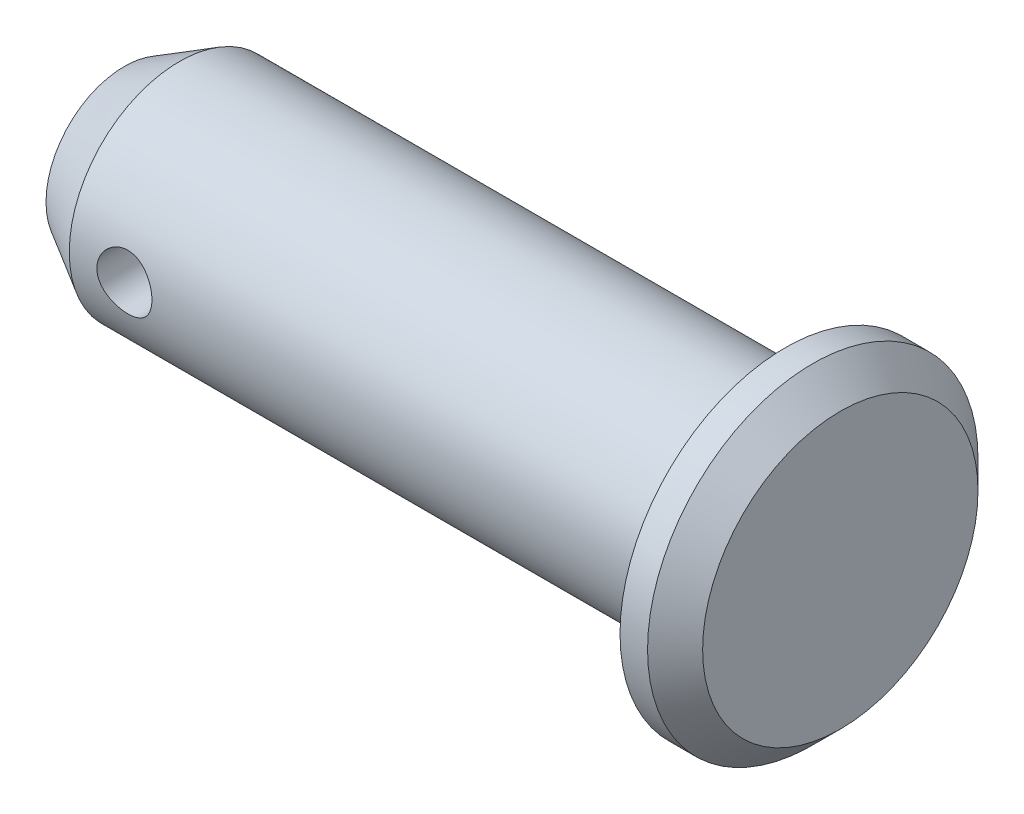
SolidWorks part; units mm, degrees
material "Plain Carbon Steel"
ref_plane "Front" through (0, 0, 0) normal (0, 0, 1) x (1, 0, 0)
ref_plane "Top" through (0, 0, 0) normal (0, 1, 0) x (1, 0, 0)
ref_plane "Right" through (0, 0, 0) normal (1, 0, 0) x (0, 0, -1)
sketch "Sketch1" plane through (0, 0, 0) normal (0, 0, 1) x (1, 0, 0)
  line L0 (0, 0) -> (-74.8754, 0) construction
  line L1 (0, 0) -> (-12, 0)
  line L2 (0, 0) -> (0, 2)
  line L3 (0, 2) -> (-12, 2)
  line L4 (-12, 0) -> (-12, 2)
  dimension "BOSS LENGTH" = 12
  dimension "BOSS DIA" = 4
revolve "Body Revolve" add sketch "Sketch1" angle 360 about L0
sketch "Sketch14" plane through (0, 0, 0) normal (0, 0, 1) x (1, 0, 0)
  line L0 (0, -2) -> (0, 2) construction
  line L1 (0, 0) -> (1, 0)
  line L2 (0, 0) -> (0, 3)
  line L3 (0, 3) -> (0.5, 3)
  line L4 (1, 0) -> (1, 2.5)
  line L5 (0, 0) -> (3.8052, 0) construction
  line L6 (0.5, 3) -> (1, 2.5)
  point P1 (1, 3)
  dimension "D1" = 6
  dimension "D2" = 1
revolve "Head Revolve" add sketch "Sketch14" angle 360 about L5
chamfer "Head Chamfer" distance 1 angle 30 1 edges at (-12, 0, -2)
sketch "Sketch21" plane through (0, 0, 0) normal (0, 0, 1) x (1, 0, 0)
  line L0 (0, 0) -> (-10, 0) construction
  circle A0 centre (-10, 0) radius 0.5
  dimension "D1" = 10
  dimension "D2" = 1
extrude "R Clip Hole" cut sketch "Sketch21" against normal through all both and the other way through all
